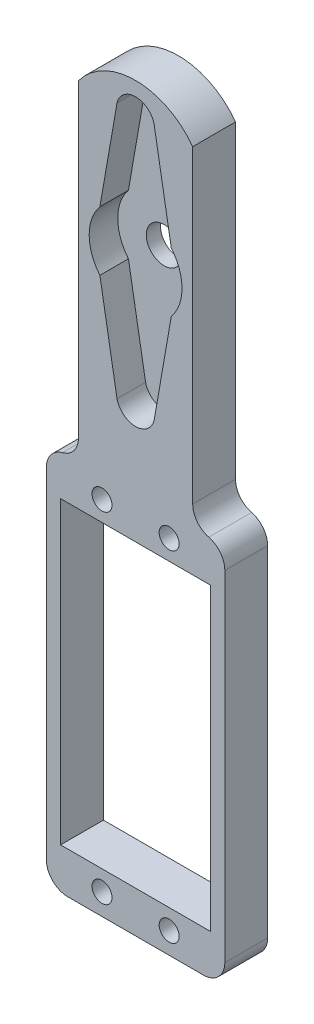
SolidWorks part; units mm, degrees
ref_plane "前基準面" through (0, 0, 0) normal (0, 0, 1) x (1, 0, 0)
ref_plane "上基準面" through (0, 0, 0) normal (0, 1, 0) x (1, 0, 0)
ref_plane "右基準面" through (0, 0, 0) normal (1, 0, 0) x (0, 0, -1)
sketch "草圖1" plane through (0, 0, 0) normal (0, 0, 1) x (1, 0, 0)
  line L1 (0, -55) -> (0, 55) construction
  line L2 (-5, 4.15) -> (-2.6, 17.9428)
  line L3 (2.6, 17.9428) -> (5, 4.15)
  line L4 (2.6, -17.9428) -> (5, -4.15)
  line L5 (-5, -4.15) -> (-2.6, -17.9428)
  line L6 (55, 0) -> (-55, 0) construction
  line L8 (-12.5, -55) -> (12.5, -55) construction
  line L12 (3.5805, 18.1413) -> (3.615, 17.9428)
  line L13 (-10.5, -34) -> (10.5, -34)
  line L14 (-5.9852, 4.3214) -> (-3.5805, 18.1413) construction
  line L15 (3.5805, 18.1413) -> (5.9852, 4.3214) construction
  line L17 (3.615, 17.9428) -> (-3.615, 17.9428)
  line L18 (8, 17.9428) -> (8, -18.1413)
  line L20 (-8, 17.9428) -> (-8, -18.1413)
  line L21 (-3.615, 17.9428) -> (-3.5805, 18.1413)
  line L22 (-10.5, -34) -> (-10.5, -76)
  line L23 (-10.5, -76) -> (10.5, -76)
  line L24 (10.5, -34) -> (10.5, -76)
  line L25 (-12.5, -28.2067) -> (-8, -28.2067)
  line L26 (-12.5, -28.2067) -> (-12.5, -81.7933)
  line L27 (-12.5, -81.7933) -> (12.5, -81.7933)
  line L28 (12.5, -28.2067) -> (12.5, -81.7933)
  line L29 (-8, -18.1413) -> (-8, -28.2067)
  line L31 (8, -28.2067) -> (8, -18.1413)
  line L32 (8, -28.2067) -> (12.5, -28.2067)
  arc A0 (-4.9993, 4.1542) -> (-4.9993, -4.1542) centre (0, 0) ccw
  arc A3 (-2.6, 17.9428) -> (2.6, 17.9428) centre (0, 17.3284) cw
  arc A4 (-2.6, -17.9428) -> (2.6, -17.9428) centre (0, -17.3284) ccw
  arc A5 (4.9993, -4.1542) -> (4.9993, 4.1542) centre (0, 0) ccw
  circle A6 centre (-4.7, -31.2) radius 1.4
  circle A11 centre (4.7, -31.2) radius 1.4
  arc A14 (-3.5805, 18.1413) -> (3.5805, 18.1413) centre (0, 17.3284) cw construction
  circle A15 centre (4.7, -78.8) radius 1.4
  circle A16 centre (-4.7, -78.8) radius 1.4
  arc A17 (-8, 17.9428) -> (8, 17.9428) centre (0, 12.0481) cw
  point P10 (0, 20)
  dimension "D1" = 5
  dimension "D2" = 14
  dimension "D3" = 14
  dimension "D9" = 13
  dimension "D11" = 42
  dimension "D16" = 2.8
  dimension "D20" = 2.8
  dimension "D4" = 5
  dimension "D5" = 2.6
  dimension "D6" = 20
  dimension "D7" = 2.6
  dimension "D8" = 34
  dimension "D10" = 1
  dimension "D12" = 21
  dimension "D13" = 10.5
  dimension "D14" = 2
  dimension "D15" = 2
  dimension "D17" = 2.8
  dimension "D18" = 5.8
  dimension "D19" = 5.8
extrude "填料-伸長1" add sketch "草圖1" along normal blind 6
fillet "圓角6" radius 3 1 edges at (-12.5, -81.7933, 3)
fillet "圓角7" radius 3 1 edges at (12.5, -81.7933, 3)
fillet "圓角8" radius 3 1 edges at (12.5, -28.2067, 3)
fillet "圓角9" radius 3 1 edges at (8, -28.2067, 3)
fillet "圓角10" radius 3 1 edges at (-12.5, -28.2067, 3)
fillet "圓角11" radius 3 1 edges at (-8, -28.2067, 3)
sketch "草圖2" plane through (0, 0, 0) normal (0, 0, 1) x (1, 0, 0)
  line L1 (-3.7023, 20.1723) -> (4.4976, 20.1723)
  line L2 (-6.6467, 17.4711) -> (-6.6467, -20.6283)
  line L3 (-6.6467, -20.6283) -> (7.0328, -20.6283)
  line L4 (7.0328, 17.4076) -> (7.0328, -20.6283)
  circle A0 centre (0, 0) radius 2.5
  arc A1 (-6.6467, 17.4711) -> (-3.7023, 20.1723) centre (-3.3588, 16.8425) cw
  arc A2 (4.4976, 20.1723) -> (7.0328, 17.4076) centre (2.7686, 16.042) cw
  point P3 (0, 0)
  point P6 (0, 0)
  point P9 (-3.7023, 20.1723)
  point P14 (0, 0)
  point P15 (-3.6177, 19.3014)
extrude "填料-伸長2" add sketch "草圖2" along normal blind 2
